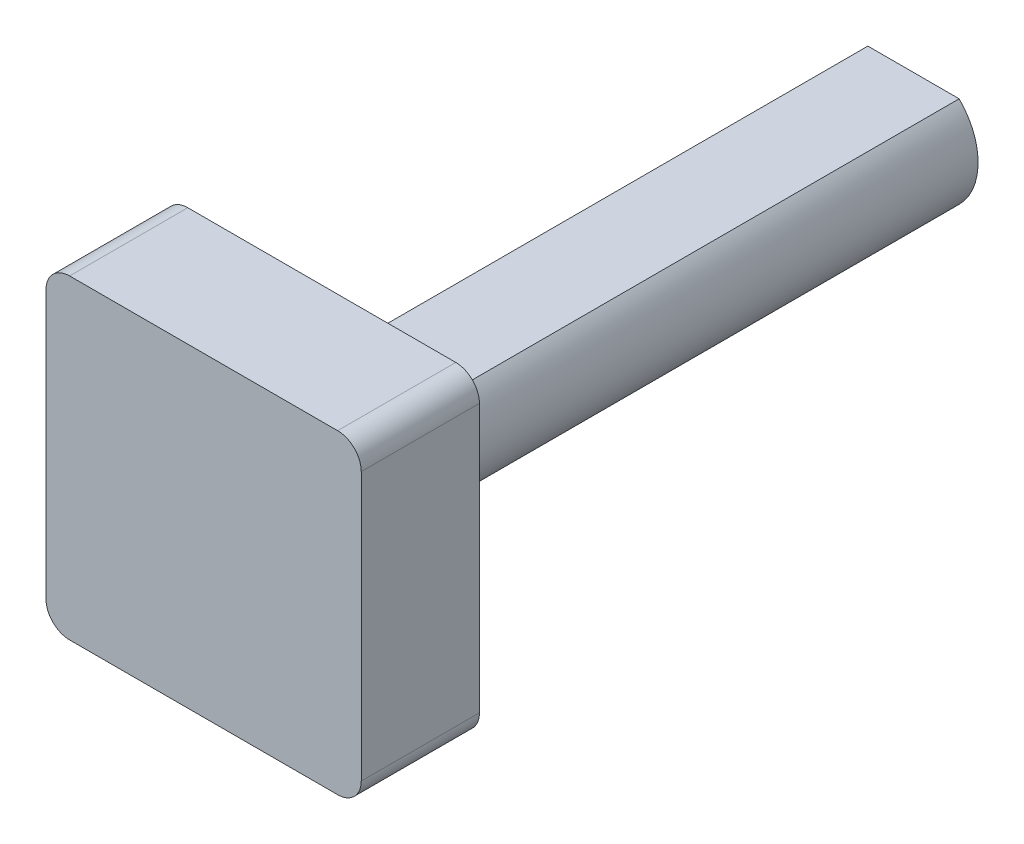
SolidWorks part; units mm, degrees
ref_plane "Front Plane" through (0, 0, 0) normal (0, 0, 1) x (1, 0, 0)
ref_plane "Top Plane" through (0, 0, 0) normal (0, 1, 0) x (1, 0, 0)
ref_plane "Right Plane" through (0, 0, 0) normal (1, 0, 0) x (0, 0, -1)
sketch "Sketch1" plane through (0, 0, 0) normal (0, 0, 1) x (1, 0, 0)
  line L3 (-21.7016, -25.3381) -> (21.5011, -25.3381)
  line L4 (-25.5116, -21.5281) -> (-25.5116, 21.6746)
  line L5 (-21.7016, 25.4846) -> (21.5011, 25.4846)
  line L6 (25.3111, -21.5281) -> (25.3111, 21.6746)
  line L7 (-25.5116, -25.3381) -> (25.3111, 25.4846) construction
  line L8 (-25.5116, 25.4846) -> (25.3111, -25.3381) construction
  arc A3 (-25.5116, 21.6746) -> (-21.7016, 25.4846) centre (-21.7016, 21.6746) cw
  arc A4 (21.5011, -25.3381) -> (25.3111, -21.5281) centre (21.5011, -21.5281) ccw
  arc A5 (25.3111, 21.6746) -> (21.5011, 25.4846) centre (21.5011, 21.6746) ccw
  arc A6 (-21.7016, -25.3381) -> (-25.5116, -21.5281) centre (-21.7016, -21.5281) cw
  dimension "D1" = 3.81
  dimension "D2" = 3.81
  dimension "D3" = 3.81
  dimension "D4" = 3.81
sketch "Sketch2" plane through (0, 0, 0) normal (0, 0, 1) x (1, 0, 0)
  line L0 (-7.3196, -7.1197) -> (7.3993, -7.1197)
  line L1 (-7.3196, 7.6166) -> (7.3993, 7.6166)
  arc A0 (-7.3196, 7.6166) -> (-7.3196, -7.1197) centre (0.0398, 0.2484) ccw
  arc A1 (7.3993, -7.1197) -> (7.3993, 7.6166) centre (0.0398, 0.2484) ccw
extrude "Boss-Extrude1" add sketch "Sketch2" against normal blind 114.3
extrude "Boss-Extrude2" add sketch "Sketch1" against normal blind 19.05
